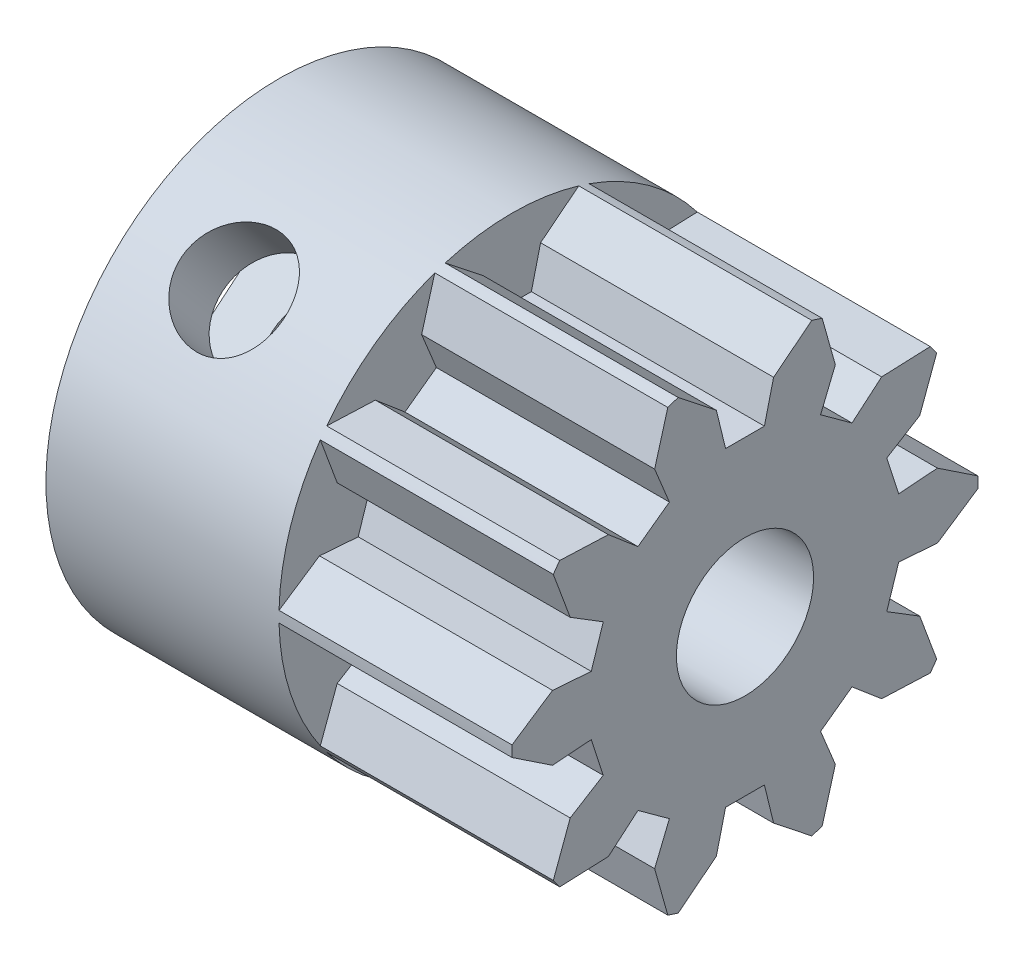
SolidWorks part; units mm, degrees
ref_plane "Plan de face" through (0, 0, 0) normal (0, 0, 1) x (1, 0, 0)
ref_plane "Plan de dessus" through (0, 0, 0) normal (0, 1, 0) x (1, 0, 0)
ref_plane "Plan de droite" through (0, 0, 0) normal (1, 0, 0) x (0, 0, -1)
sketch "Esquisse1" plane through (0, 0, 0) normal (1, 0, 0) x (0, 0, -1)
  circle A0 centre (0, 0) radius 9
  circle A1 centre (0, 0) radius 2.65
  dimension "D1" = 18
  dimension "D2" = 5.3
extrude "Boss.-Extru.1" add sketch "Esquisse1" along normal blind 18
sketch "Esquisse5" plane through (18, 0, 0) normal (1, 0, 0) x (0, 0, -1)
  line L0 (-0.75, 6) -> (0.75, 6)
  line L1 (0, 0) -> (0, 9) construction
  line L2 (-1.105, 7.4574) -> (1.105, 7.4574) construction
  line L3 (2.5796, 8.6224) -> (-2.5796, 8.6224) construction
  line L4 (-0.75, 6) -> (-1.105, 7.4574)
  line L5 (-1.105, 7.4574) -> (-2.5796, 8.6224)
  line L6 (0.75, 6) -> (1.105, 7.4574)
  line L7 (1.105, 7.4574) -> (2.5796, 8.6224)
  circle A0 centre (0, 0) radius 9 construction
  arc A1 (-2.5796, 8.6224) -> (2.5796, 8.6224) centre (0, 0) cw
  point P8 (0, 6)
  dimension "D1" = 1.5
  dimension "D2" = 3
  dimension "D3" = 1.5
  dimension "D4" = 142
  dimension "D5" = 2.21
extrude "Enlèv. mat.-Extru.2" cut sketch "Esquisse5" against normal blind 9
pattern_circular "Répétition circulaire1" count 10 over 360 about axis through (0, 0, 0) along (1, 0, 0) of "Enlèv. mat.-Extru.2"
sketch "Esquisse6" plane through (0, 0, 0) normal (-1, 0, 0) x (0, 0, 1)
  line L0 (-9, 0) -> (0, 0) construction
  line L2 (-6.5, 3) -> (-3.5, 3)
  line L3 (-6.5, 3) -> (-6.5, -3)
  line L4 (-6.5, -3) -> (-3.5, -3)
  line L5 (-3.5, 3) -> (-3.5, -3)
  line L6 (-6.5, 3) -> (-3.5, -3) construction
  line L7 (-6.5, -3) -> (-3.5, 3) construction
  circle A0 centre (0, 0) radius 9 construction
  point P5 (-5, 0)
  dimension "D1" = 6
  dimension "D2" = 3
  dimension "D3" = 2.5
extrude "Enlèv. mat.-Extru.3" cut sketch "Esquisse6" against normal blind 7
ref_plane "Plan1" through (0, 0, -9) normal (0, 0, -1) x (-1, 0, 0)
sketch "Esquisse7" plane through (0, 0, -9) normal (0, 0, -1) x (-1, 0, 0)
  line L0 (-4, 0) -> (0, 0) construction
  circle A0 centre (-4, 0) radius 2
  dimension "D2" = 4
  dimension "D1" = 4
extrude "Enlèv. mat.-Extru.4" cut sketch "Esquisse7" against normal blind 9
pattern_circular "Répétition circulaire2" count 2 over 130 about axis through (0, 0, 0) along (1, 0, 0) of "Enlèv. mat.-Extru.4", "Enlèv. mat.-Extru.3"
